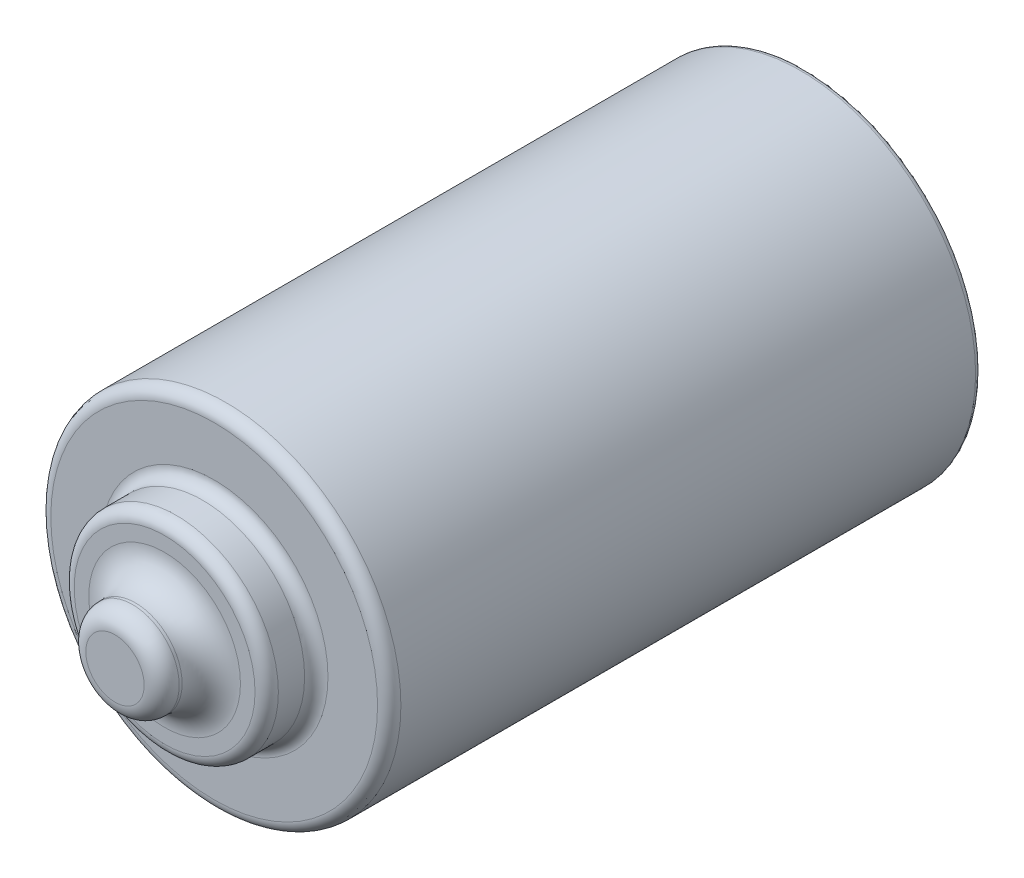
SolidWorks part; units mm, degrees
ref_plane "Alzado" through (0, 0, 0) normal (0, 0, 1) x (1, 0, 0)
ref_plane "Planta" through (0, 0, 0) normal (0, 1, 0) x (1, 0, 0)
ref_plane "Vista lateral" through (0, 0, 0) normal (1, 0, 0) x (0, 0, -1)
sketch "Croquis1" plane through (0, 0, 0) normal (0, 0, 1) x (1, 0, 0)
  circle A0 centre (0, 0) radius 30
  dimension "D1" = 60
extrude "Saliente-Extruir1" add sketch "Croquis1" along normal blind 101.5 contours A0
sketch "Croquis2" plane through (0, 0, 101.5) normal (0, 0, 1) x (1, 0, 0)
  circle A0 centre (0, 0) radius 17.5
extrude "Saliente-Extruir2" add sketch "Croquis2" along normal blind 8.5
sketch "Croquis3" plane through (0, 0, 110) normal (0, 0, 1) x (1, 0, 0)
  circle A0 centre (0, 0) radius 8
extrude "Saliente-Extruir3" add sketch "Croquis3" along normal blind 8.5 contours A0
sketch "Croquis4" plane through (0, 0, 0) normal (0, 0, -1) x (-1, 0, 0)
  circle A0 centre (0, 0) radius 16
extrude "Saliente-Extruir4" add sketch "Croquis4" along normal blind 2.5 contours A0
fillet "Redondeo1" radius 2 1 edges at (30, 0, 101.5)
fillet "Redondeo2" radius 2 1 edges at (17.5, 0, 101.5)
fillet "Redondeo3" radius 2 1 edges at (17.5, 0, 110)
fillet "Redondeo4" radius 5 1 edges at (8, 0, 110)
fillet "Redondeo5" radius 3 1 edges at (8, 0, 118.5)
fillet "Redondeo6" radius 1 1 edges at (30, 0, 0)
fillet "Redondeo7" radius 1 1 edges at (-16, 0, -2.5)
